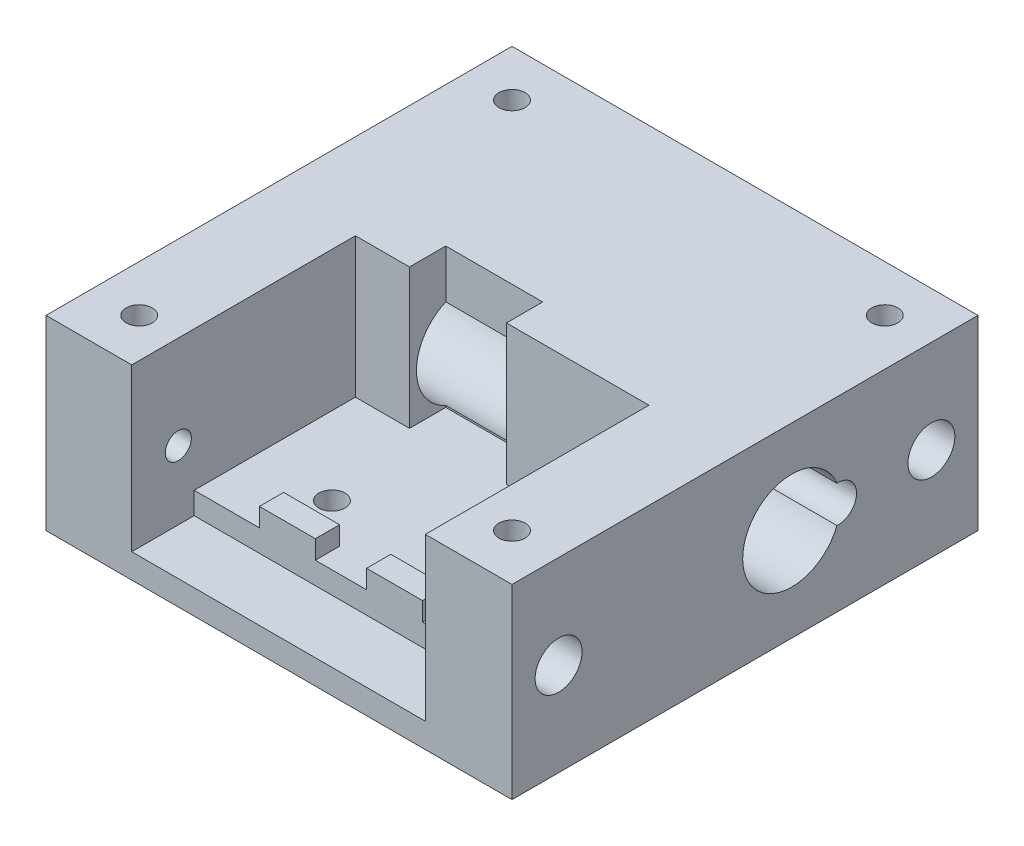
SolidWorks part; units mm, degrees
ref_plane "Front Plane" through (0, 0, 0) normal (0, 0, 1) x (1, 0, 0)
ref_plane "Top Plane" through (0, 0, 0) normal (0, 1, 0) x (1, 0, 0)
ref_plane "Right Plane" through (0, 0, 0) normal (1, 0, 0) x (0, 0, -1)
sketch "Sketch1" plane through (0, 0, 0) normal (0, 1, 0) x (1, 0, 0)
  line L1 (0, 0) -> (31.75, 0)
  line L2 (0, 0) -> (0, 31.75)
  line L3 (0, 31.75) -> (31.75, 31.75)
  line L4 (31.75, 0) -> (31.75, 31.75)
  dimension "D1" = 31.75
  dimension "D2" = 31.75
extrude "Main body" add sketch "Sketch1" along normal blind 12.7
sketch "Sketch2" plane through (0, 12.7, 0) normal (0, 1, 0) x (1, 0, 0)
  line L0 (5.842, 0) -> (5.842, 15.24)
  line L1 (0, 0) -> (31.75, 0) construction
  line L2 (5.842, 15.24) -> (9.525, 15.24)
  line L3 (9.525, 15.24) -> (9.525, 17.7127)
  line L4 (9.525, 17.7127) -> (16.129, 17.7127)
  line L5 (16.129, 17.7127) -> (16.129, 15.24)
  line L6 (16.129, 15.24) -> (25.842, 15.24)
  line L7 (25.842, 15.24) -> (25.842, 0)
  line L8 (25.842, 0) -> (5.842, 0)
  line L9 (0, 31.75) -> (0, 0) construction
  dimension "D1" = 20
  dimension "D2" = 5.842
  dimension "D3" = 15.24
  dimension "D4" = 9.525
  dimension "D5" = 6.604
extrude "Cut-Extrude1" cut sketch "Sketch2" against normal blind 9.525
sketch "Sketch3" plane through (0, 3.175, 0) normal (0, 1, 0) x (1, 0, 0)
  line L0 (25.842, 0) -> (25.842, 15.24) construction
  line L1 (5.842, 0) -> (25.842, 0)
  line L2 (5.842, 0) -> (5.842, 4.2545)
  line L3 (5.842, 4.2545) -> (25.842, 4.2545)
  line L4 (25.842, 0) -> (25.842, 4.2545)
  dimension "D1" = 4.2545
extrude "Cut-Extrude2" cut sketch "Sketch3" against normal blind 1.5
sketch "Sketch4" plane through (0, 3.175, 0) normal (0, 1, 0) x (1, 0, 0)
  line L0 (25.842, 4.2545) -> (5.842, 4.2545) construction
  line L1 (10.287, 4.2545) -> (14.097, 4.2545)
  line L2 (10.287, 4.2545) -> (10.287, 5.9055)
  line L3 (10.287, 5.9055) -> (14.097, 5.9055)
  line L4 (14.097, 4.2545) -> (14.097, 5.9055)
  line L5 (5.842, 15.24) -> (5.842, 4.2545) construction
  line L6 (17.587, 4.2545) -> (21.397, 4.2545)
  line L7 (17.587, 4.2545) -> (17.587, 5.9055)
  line L8 (17.587, 5.9055) -> (21.397, 5.9055)
  line L9 (21.397, 4.2545) -> (21.397, 5.9055)
  line L10 (25.842, 4.2545) -> (25.842, 15.24) construction
  point P12 (12.192, 4.2545)
  point P13 (19.492, 4.2545)
  dimension "D1" = 6.35
  dimension "D2" = 6.35
  dimension "D3" = 3.81
  dimension "D4" = 3.81
  dimension "D5" = 1.651
extrude "Boss-Extrude2" add sketch "Sketch4" along normal blind 1.27
sketch "Sketch5" plane through (0, 0, 0) normal (-1, 0, 0) x (0, 0, 1)
  line L0 (0, 12.7) -> (0, 0) construction
  line L1 (-31.75, 6.35) -> (0, 6.35) construction
  line L2 (-31.75, 12.7) -> (-31.75, 0) construction
  circle A0 centre (-19.05, 6.35) radius 3.3337
  arc A3 (-15.7163, 6.35) -> (-22.3837, 6.35) centre (-19.05, 6.35) ccw construction
  arc A4 (-22.3837, 6.35) -> (-15.7163, 6.35) centre (-19.05, 6.35) ccw construction
  dimension "D1" = 19.05
  dimension "D2" = 6.6675
extrude "Cut-Extrude3" cut sketch "Sketch5" against normal through all
sketch "Sketch17" [suppressed] plane through (0, 0, 0) normal (1, 0, 0) x (0, 0, -1)
  circle A2 centre (19.05, 6.35) radius 3.175 construction
  arc A3 (22.3828, 5.11) -> (22.3828, 7.59) centre (22.225, 6.35) ccw
  arc A4 (22.3828, 7.59) -> (22.3828, 5.11) centre (19.05, 6.35) ccw
  arc A5 (22.3828, 5.11) -> (22.3828, 7.59) centre (19.05, 6.35) ccw construction
  arc A6 (22.3828, 7.59) -> (21.9789, 7.5755) centre (22.225, 6.35) ccw construction
  arc A7 (21.9789, 7.5755) -> (21.9789, 5.1245) centre (22.225, 6.35) ccw construction
  arc A8 (21.9789, 5.1245) -> (22.3828, 5.11) centre (22.225, 6.35) ccw construction
  dimension "D1" = 6.35
  dimension "D2" = 7.112
extrude "Cut-Extrude7" [suppressed] cut sketch "Sketch17" along normal blind 7.62
sketch "Sketch6" plane through (31.75, 0, 0) normal (-1, 0, 0) x (0, 0, 1)
  line L0 (-22.225, 6.35) -> (-15.875, 6.35) construction
  circle A0 centre (-19.05, 6.35) radius 3.175 construction
  circle A1 centre (-22.225, 6.35) radius 1.25
  dimension "D1" = 2.5
  dimension "D2" = 6.35
extrude "Cut-Extrude4" cut sketch "Sketch6" along normal blind 20.32 contours A1
chamfer "Chamfer3" [suppressed] distance 1.27 angle 45
hole_wizard "Tap Drill for #2-56 Tap1" positions "Sketch8" profile "Sketch9" hole size "#2-56" standard "ANSI Inch" end condition through all
sketch "Sketch8" plane through (0, 0, 0) normal (0, -1, 0) x (-1, 0, 0)
  line L0 (-31.75, 31.75) -> (0, 0) construction
  line L3 (-3.175, 3.175) -> (-28.575, 3.175)
  line L4 (-3.175, 3.175) -> (-3.175, 28.575)
  line L5 (-3.175, 28.575) -> (-28.575, 28.575)
  line L6 (-28.575, 3.175) -> (-28.575, 28.575)
  line L7 (-3.175, 3.175) -> (-28.575, 28.575) construction
  line L8 (-3.175, 28.575) -> (-28.575, 3.175) construction
  point P7 (-28.575, 28.575)
  point P196 (-3.175, 3.175)
  point P197 (-3.175, 28.575)
  point P198 (-28.575, 3.175)
  dimension "D1" = 25.4
sketch "Sketch9" plane through (28.575, 0, -3.175) normal (1, 0, 0) x (0, 0, -1)
  line L0 (0, 0) -> (0, 12.7)
  line L1 (0, 12.7) -> (0.889, 12.7)
  line L2 (0.889, 12.7) -> (0.889, 0)
  line L5 (0.889, 0) -> (0, 0)
  line L11 (0, -6.35) -> (0, 107.95) construction
  dimension "Thru Hole Dia." = 1.778
  dimension "Thru Hole Depth" = 12.7
hole_wizard "Tap Drill for #2-56 Tap2" positions "Sketch10" profile "Sketch11" hole size "#2-56" standard "ANSI Inch" end condition through all
sketch "Sketch10" plane through (0, 3.175, 0) normal (0, 1, 0) x (1, 0, 0)
  line L0 (5.842, 8.34) -> (25.842, 8.34) construction
  line L1 (5.842, 15.24) -> (5.842, 4.2545) construction
  line L2 (25.842, 4.2545) -> (25.842, 15.24) construction
  line L5 (25.842, 15.24) -> (16.129, 15.24) construction
  point P12 (11.142, 8.34)
  point P14 (20.642, 8.34)
  dimension "D1" = 6.9
  dimension "D2" = 9.5
  dimension "D3" = 5.2
sketch "Sketch11" plane through (20.642, 3.175, -8.34) normal (1, 0, 0) x (0, 0, 1)
  line L0 (0, 0) -> (0, 3.175)
  line L1 (0, 3.175) -> (0.889, 3.175)
  line L2 (0.889, 3.175) -> (0.889, 0)
  line L5 (0.889, 0) -> (0, 0)
  line L11 (0, -6.35) -> (0, 107.95) construction
  dimension "Thru Hole Dia." = 1.778
  dimension "Thru Hole Depth" = 3.175
hole_wizard "Ø3.2 (3.2) Diameter Hole1" positions "Sketch12" profile "Sketch13" hole size "Ø3.2" standard "ANSI Metric"
sketch "Sketch12" plane through (31.75, 0, 0) normal (1, 0, 0) x (0, 0, -1)
  line L0 (0, 6.35) -> (31.75, 6.35) construction
  line L1 (0, 12.7) -> (0, 0) construction
  line L2 (31.75, 12.7) -> (31.75, 0) construction
  point P9 (3.175, 6.35)
  point P11 (28.575, 6.35)
  dimension "D1" = 3.175
  dimension "D2" = 25.4
sketch "Sketch13" plane through (31.75, 6.35, -28.575) normal (0, 1, 0) x (0, 0, -1)
  line L0 (0, 0) -> (0, 7.112)
  line L1 (0, 7.112) -> (1.6, 6.1506)
  line L2 (1.6, 6.1506) -> (1.6, 0)
  line L5 (1.6, 0) -> (0, 0)
  line L10 (0, 7.112) -> (-1.6, 6.1506) construction
  line L11 (0, -6.35) -> (0, 107.95) construction
  dimension "Hole Dia." = 3.2
  dimension "Hole Depth" = 7.112
  dimension "Drill Angle" = 118
hole_wizard "Tap Drill for #2-56 Tap4" positions "Sketch14" profile "Sketch15" hole size "#2-56" standard "ANSI Inch"
sketch "Sketch14" plane through (0, 0, 0) normal (-1, 0, 0) x (0, 0, 1)
  line L0 (-31.75, 6.35) -> (0, 6.35) construction
  line L1 (-31.75, 12.7) -> (-31.75, 0) construction
  line L2 (0, 12.7) -> (0, 0) construction
  point P9 (-28.575, 6.35)
  point P11 (-3.175, 6.35)
  dimension "D1" = 3.175
  dimension "D2" = 3.175
sketch "Sketch15" plane through (0, 6.35, -3.175) normal (0, 1, 0) x (0, 0, 1)
  line L0 (0, 0) -> (0, 7.112)
  line L1 (0, 7.112) -> (0.889, 6.5778)
  line L2 (0.889, 6.5778) -> (0.889, 0)
  line L5 (0.889, 0) -> (0, 0)
  line L10 (0, 7.112) -> (-0.889, 6.5778) construction
  line L11 (0, -6.35) -> (0, 107.95) construction
  dimension "Hole Dia." = 1.778
  dimension "Hole Depth" = 7.112
  dimension "Drill Angle" = 118
